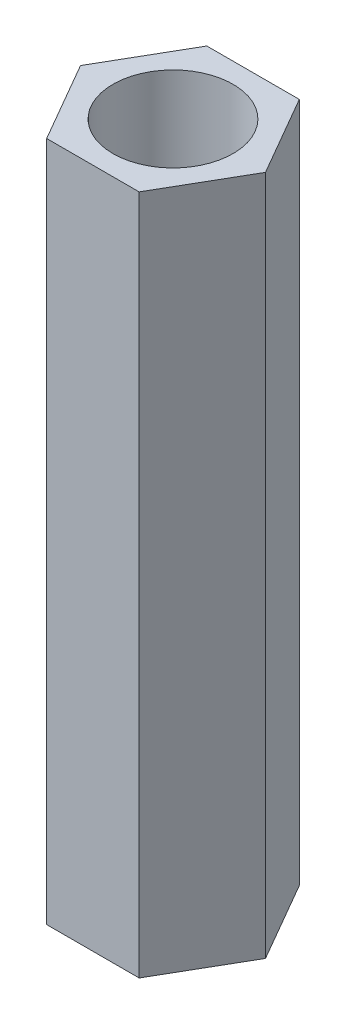
SolidWorks part; units mm, degrees
material "Commercial Bronze, UNS C22000 (90-10 Bronze)"
ref_plane "Alzado" through (0, 0, 0) normal (0, 0, 1) x (1, 0, 0)
ref_plane "Planta" through (0, 0, 0) normal (0, 1, 0) x (1, 0, 0)
ref_plane "Vista lateral" through (0, 0, 0) normal (1, 0, 0) x (0, 0, -1)
sketch "Croquis1" plane through (0, 0, 0) normal (0, 1, 0) x (1, 0, 0)
  line L1 (1.1547, 2) -> (-1.1547, 2)
  line L2 (-1.1547, 2) -> (-2.3094, 0)
  line L3 (-2.3094, 0) -> (-1.1547, -2)
  line L4 (-1.1547, -2) -> (1.1547, -2)
  line L5 (1.1547, -2) -> (2.3094, 0)
  line L6 (2.3094, 0) -> (1.1547, 2)
  circle A0 centre (0, 0) radius 2 construction
  circle A1 centre (0, 0) radius 1.5
  dimension "D1" = 4
  dimension "D2" = 3
extrude "Saliente-Extruir1" add sketch "Croquis1" along normal mid plane 17
